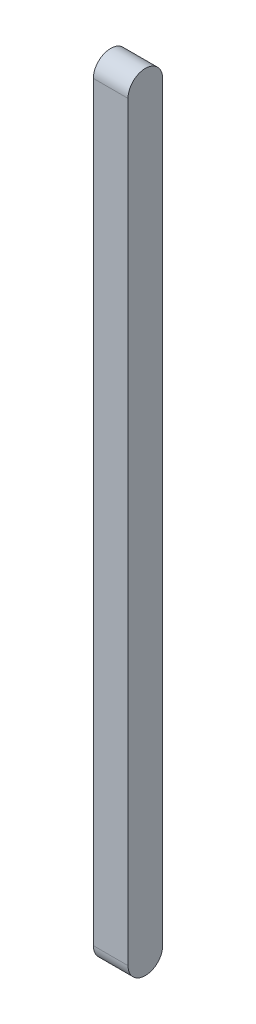
SolidWorks part; units mm, degrees
ref_plane "Front Plane" through (0, 0, 0) normal (0, 0, 1) x (1, 0, 0)
ref_plane "Top Plane" through (0, 0, 0) normal (0, 1, 0) x (1, 0, 0)
ref_plane "Right Plane" through (0, 0, 0) normal (1, 0, 0) x (0, 0, -1)
sketch "Sketch1" plane through (0, 0, 0) normal (0, 1, 0) x (1, 0, 0)
  line L1 (-15, 15) -> (15, 15)
  line L2 (-15, 15) -> (-15, -15)
  line L3 (-15, -15) -> (15, -15)
  line L4 (15, 15) -> (15, -15)
  line L5 (-15, 15) -> (15, -15) construction
  line L6 (-15, -15) -> (15, 15) construction
  point P0 (0, 0)
  dimension "D1" = 30
  dimension "D2" = 30
extrude "Boss-Extrude1" add sketch "Sketch1" along normal blind 650
sketch "Sketch2" plane through (-15, 0, 0) normal (-1, 0, 0) x (0, 0, 1)
  line L0 (-15, 0) -> (15, 0) construction
  line L1 (-15, 650) -> (15, 650) construction
  circle A0 centre (0, 0) radius 15
  circle A1 centre (0, 650) radius 15
extrude "Boss-Extrude2" add sketch "Sketch2" against normal blind 30
